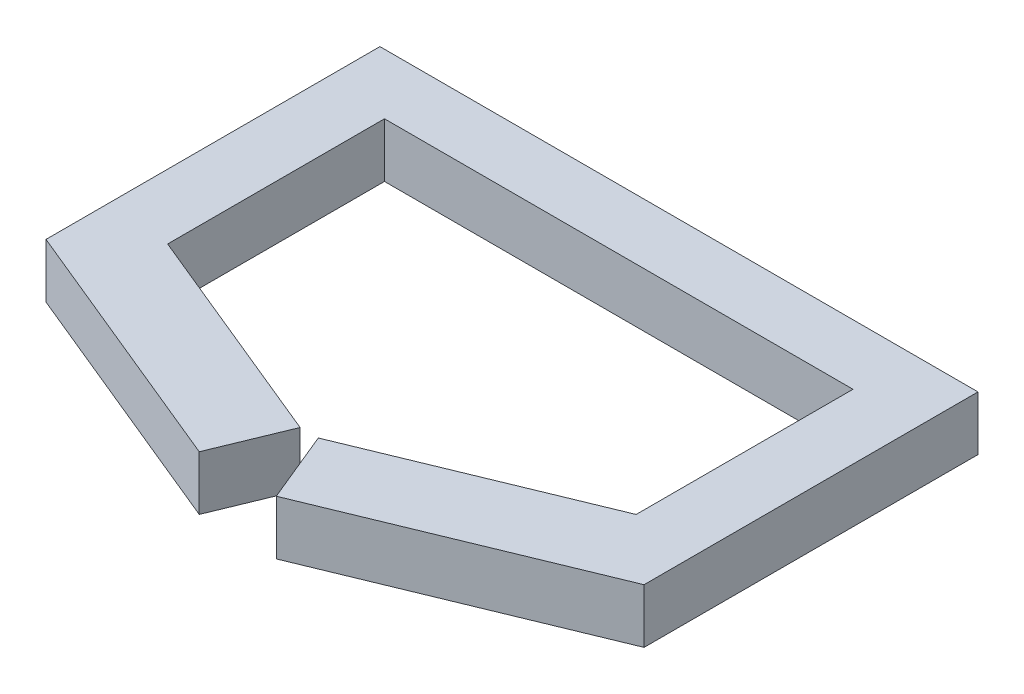
SolidWorks part; units mm, degrees
ref_plane "Front Plane" through (0, 0, 0) normal (0, 0, 1) x (1, 0, 0)
ref_plane "Top Plane" through (0, 0, 0) normal (0, 1, 0) x (1, 0, 0)
ref_plane "Right Plane" through (0, 0, 0) normal (1, 0, 0) x (0, 0, -1)
sketch "Sketch1" plane through (0, 0, 0) normal (0, 1, 0) x (1, 0, 0)
  line L1 (-7.0919, -47.5805) -> (-1.6763, -34.4282)
  line L2 (-1.6763, -34.4282) -> (-43.1308, -17.3587)
  line L3 (-43.1308, -17.3587) -> (-43.1308, 22.5653)
  line L4 (-43.1308, 22.5653) -> (43.1308, 22.5653)
  line L6 (55.0593, 33.6545) -> (-55.0593, 33.6545)
  line L7 (-55.0593, 33.6545) -> (-55.0593, -27.8292)
  line L8 (-55.0593, -27.8292) -> (-7.0919, -47.5805)
  line L9 (7.0919, -47.5805) -> (1.6763, -34.4282)
  line L10 (55.0593, -27.8292) -> (7.0919, -47.5805)
  line L11 (55.0593, 33.6545) -> (55.0593, -27.8292)
  line L12 (43.1308, -17.3587) -> (43.1308, 22.5653)
  line L13 (1.6763, -34.4282) -> (43.1308, -17.3587)
  point P4 (0, 0)
extrude "Boss-Extrude1" add sketch "Sketch1" along normal blind 10
